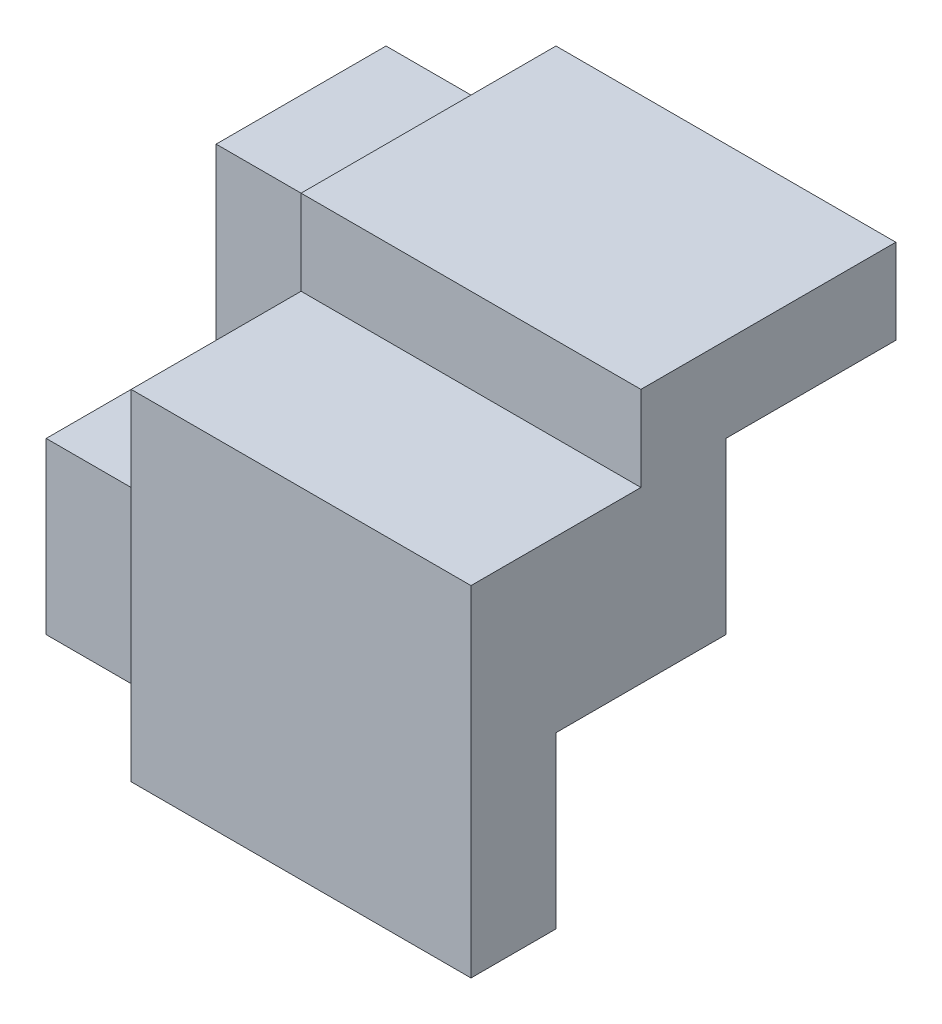
SolidWorks part; units mm, degrees
ref_plane "Front Plane" through (0, 0, 0) normal (0, 0, 1) x (1, 0, 0)
ref_plane "Top Plane" through (0, 0, 0) normal (0, 1, 0) x (1, 0, 0)
ref_plane "Right Plane" through (0, 0, 0) normal (1, 0, 0) x (0, 0, -1)
sketch "Sketch1" plane through (0, 0, 0) normal (0, 0, 1) x (1, 0, 0)
  line L1 (0, 0) -> (60, 0)
  line L2 (0, 0) -> (0, 50)
  line L3 (0, 50) -> (60, 50)
  line L4 (60, 0) -> (60, 50)
  dimension "D1" = 60
  dimension "D2" = 50
extrude "Boss-Extrude1" add sketch "Sketch1" along normal blind 50
sketch "Sketch2" plane through (0, 0, 50) normal (0, 0, 1) x (1, 0, 0)
  line L1 (0, 50) -> (20, 50)
  line L2 (0, 50) -> (0, 40)
  line L3 (0, 40) -> (20, 40)
  line L4 (20, 50) -> (20, 40)
  dimension "D1" = 20
  dimension "D2" = 10
extrude "Cut-Extrude1" cut sketch "Sketch2" against normal blind 50
sketch "Sketch3" plane through (0, 0, 50) normal (0, 0, 1) x (1, 0, 0)
  line L1 (0, 40) -> (20, 40)
  line L2 (0, 40) -> (0, 20)
  line L3 (0, 20) -> (20, 20)
  line L4 (20, 40) -> (20, 20)
  dimension "D1" = 20
  dimension "D2" = 20
extrude "Cut-Extrude2" cut sketch "Sketch3" against normal blind 20
sketch "Sketch4" plane through (0, 0, 50) normal (0, 0, 1) x (1, 0, 0)
  line L0 (20, 20) -> (20, 50) construction
  line L1 (60, 50) -> (20, 50)
  line L2 (60, 50) -> (60, 40)
  line L3 (60, 40) -> (20, 40)
  line L4 (20, 50) -> (20, 40)
  dimension "D1" = 10
extrude "Cut-Extrude3" cut sketch "Sketch4" against normal blind 30
sketch "Sketch5" plane through (0, 0, 30) normal (0, 0, 1) x (1, 0, 0)
  line L1 (20, 20) -> (0, 20)
  line L2 (20, 20) -> (20, 40)
  line L3 (20, 40) -> (0, 40)
  line L4 (0, 20) -> (0, 40)
extrude "Cut-Extrude4" cut sketch "Sketch5" against normal blind 10
sketch "Sketch6" plane through (0, 0, 50) normal (0, 0, 1) x (1, 0, 0)
  line L0 (0, 0) -> (60, 0) construction
  line L1 (0, 20) -> (20, 20)
  line L2 (0, 20) -> (0, 0)
  line L3 (0, 0) -> (20, 0)
  line L4 (20, 20) -> (20, 0)
  dimension "D1" = 20
extrude "Cut-Extrude5" cut sketch "Sketch6" against normal blind 10
ref_plane "Plane1" through (60, 50, 0) normal (0, 0, -1) x (-1, 0, 0)
sketch "Sketch8" plane through (0, 0, 20) normal (0, 0, 1) x (1, 0, 0)
  line L1 (60, 50) -> (20, 50)
  line L2 (60, 50) -> (60, 40)
  line L3 (60, 40) -> (20, 40)
  line L4 (20, 50) -> (20, 40)
extrude "Boss-Extrude2" add sketch "Sketch8" along normal blind 10
sketch "Sketch9" plane through (0, 0, 0) normal (0, -1, 0) x (-1, 0, 0)
  line L1 (-60, 0) -> (-40, 0)
  line L2 (-60, 0) -> (-60, -40)
  line L3 (-60, -40) -> (-40, -40)
  line L4 (-40, 0) -> (-40, -40)
  dimension "D1" = 20
  dimension "D2" = 40
extrude "Cut-Extrude6" cut sketch "Sketch9" against normal blind 20
sketch "Sketch10" plane through (0, 0, 0) normal (0, 0, -1) x (-1, 0, 0)
  line L0 (-60, 20) -> (-60, 50) construction
  line L1 (-40, 20) -> (-60, 20)
  line L2 (-40, 20) -> (-40, 40)
  line L3 (-40, 40) -> (-60, 40)
  line L4 (-60, 20) -> (-60, 40)
  dimension "D1" = 20
extrude "Cut-Extrude7" cut sketch "Sketch10" against normal blind 20
